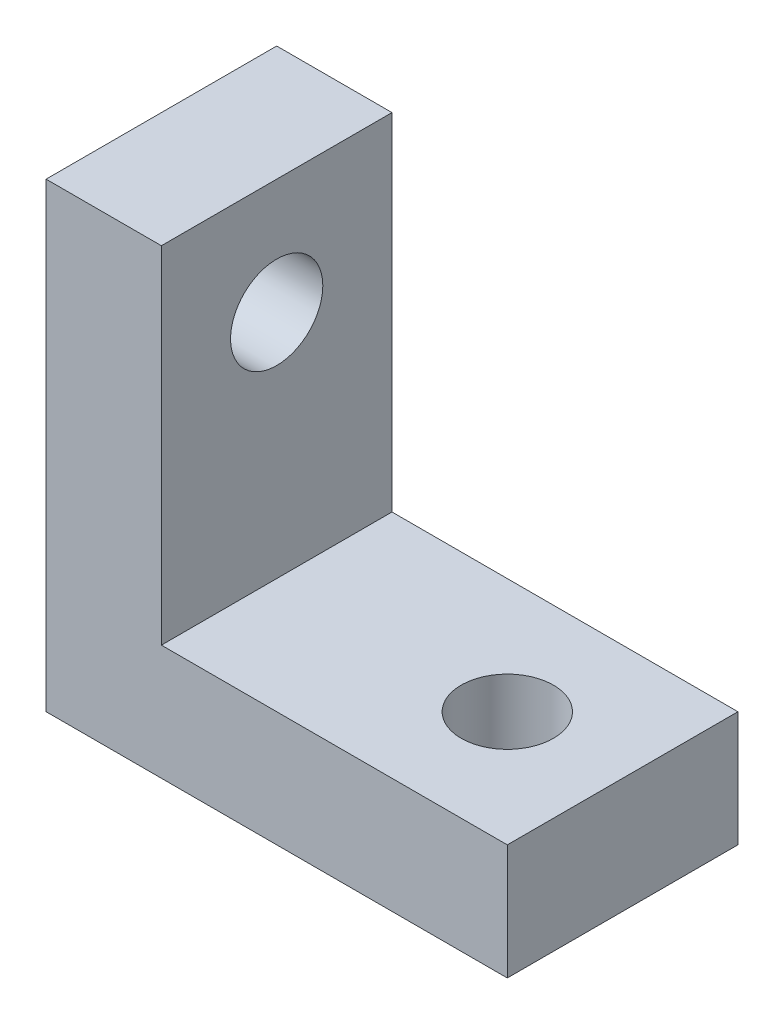
SolidWorks part; units mm, degrees
ref_plane "Front Plane" through (0, 0, 0) normal (0, 0, 1) x (1, 0, 0)
ref_plane "Top Plane" through (0, 0, 0) normal (0, 1, 0) x (1, 0, 0)
ref_plane "Right Plane" through (0, 0, 0) normal (1, 0, 0) x (0, 0, -1)
sketch "Sketch1" plane through (0, 0, 0) normal (0, 0, 1) x (1, 0, 0)
  line L2 (-4.8406, 0) -> (-4.8406, 20)
  line L3 (-4.8406, 20) -> (-9.8406, 20)
  line L4 (-9.8406, 0) -> (-9.8406, 20)
  line L5 (-9.8406, 5) -> (10.1594, 5)
  line L7 (-9.8406, 0) -> (10.1594, 0)
  line L8 (10.1594, 5) -> (10.1594, 0)
  dimension "D1" = 5
  dimension "D2" = 5
  dimension "D3" = 20
  dimension "D4" = 20
extrude "Boss-Extrude2" add sketch "Sketch1" along normal blind 10 contours L4 L5 L2 L3 | L4 L7 L2 L5 | L8 L5 L2 L7
sketch "Sketch3" plane through (0, 5, 0) normal (0, 1, 0) x (1, 0, 0)
  line L0 (10.1594, -10) -> (10.1594, 0) construction
  line L1 (-4.8406, 0) -> (10.1594, 0) construction
  circle A0 centre (5.1594, -5) radius 2
  dimension "D1" = 4
  dimension "D2" = 5
  dimension "D3" = 5
extrude "Cut-Extrude1" cut sketch "Sketch3" against normal through all
sketch "Sketch4" plane through (-4.8406, 0, 0) normal (1, 0, 0) x (0, 0, -1)
  line L0 (-10, 5) -> (-10, 20) construction
  line L1 (-10, 20) -> (0, 20) construction
  circle A0 centre (-5, 15) radius 2
  dimension "D1" = 4
  dimension "D2" = 5
  dimension "D3" = 5
extrude "Cut-Extrude2" cut sketch "Sketch4" against normal through all
